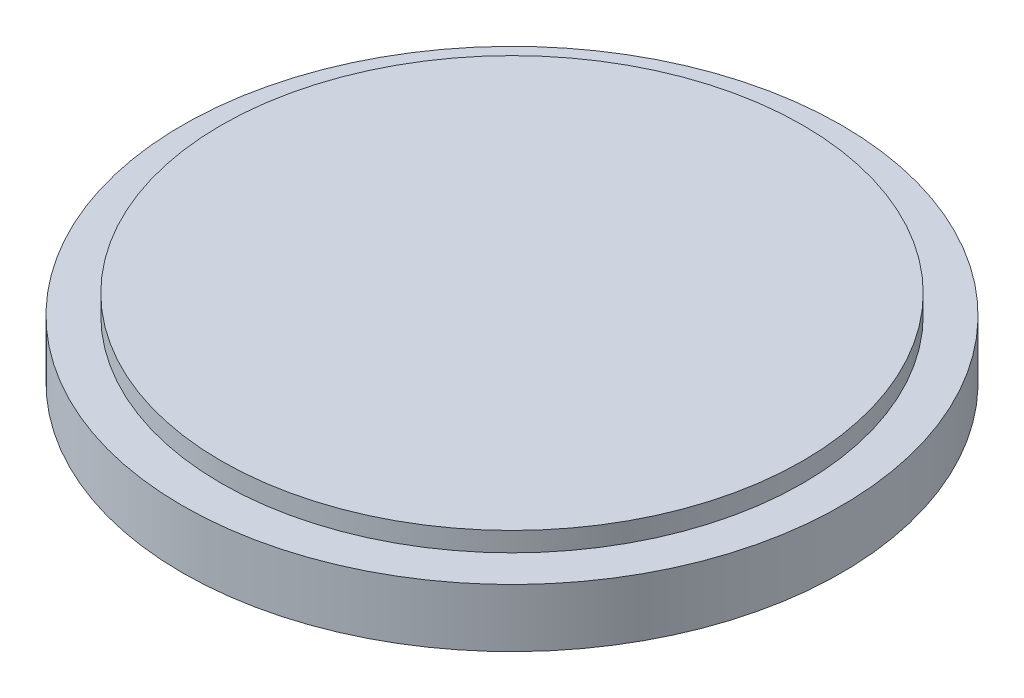
SolidWorks part; units mm, degrees
ref_plane "Front Plane" through (0, 0, 0) normal (0, 0, 1) x (1, 0, 0)
ref_plane "Top Plane" through (0, 0, 0) normal (0, 1, 0) x (1, 0, 0)
ref_plane "Right Plane" through (0, 0, 0) normal (1, 0, 0) x (0, 0, -1)
sketch "Sketch1" plane through (0, 0, 0) normal (0, 1, 0) x (1, 0, 0)
  circle A0 centre (0, 0) radius 75
  dimension "D1" = 150
extrude "Boss-Extrude1" add sketch "Sketch1" along normal blind 5
sketch "Sketch2" plane through (0, 0, 0) normal (0, -1, 0) x (1, 0, 0)
  circle A0 centre (0, 0) radius 85
  dimension "170" = 170
extrude "Boss-Extrude2" add sketch "Sketch2" along normal blind 15
